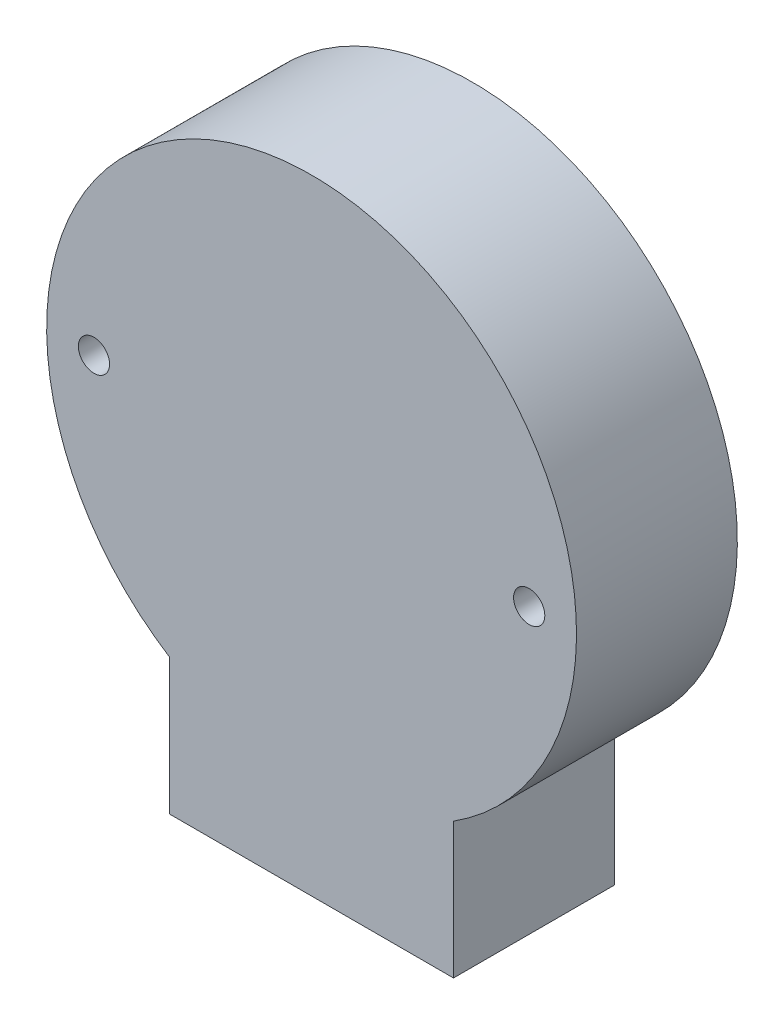
SolidWorks part; units mm, degrees
material "PF"
ref_plane "Front Plane" through (0, 0, 0) normal (0, 0, 1) x (1, 0, 0)
ref_plane "Top Plane" through (0, 0, 0) normal (0, 1, 0) x (1, 0, 0)
ref_plane "Right Plane" through (0, 0, 0) normal (1, 0, 0) x (0, 0, -1)
sketch "Sketch1" plane through (0, 0, 0) normal (0, 0, 1) x (1, 0, 0)
  line L0 (-24.6127, 28) -> (29.3258, 28) construction
  line L2 (-15, -23.6432) -> (-15, -38)
  line L3 (-15, -38) -> (15, -38)
  line L4 (15, -23.6432) -> (15, -38)
  arc A0 (15, -23.6432) -> (-15, -23.6432) centre (0, 0) ccw
  dimension "D1" = 56
  dimension "D2" = 66
  dimension "D3" = 30
extrude "Boss-Extrude1" add sketch "Sketch1" along normal blind 17
hole_wizard "Ø3.3 (3.3) Diameter Hole1" positions "Sketch3" profile "Sketch2" hole size "Ø3.3" standard "Ansi Metric"
sketch "Sketch3" plane through (0, 0, 17) normal (0, 0, 1) x (1, 0, 0)
  line L2 (-23, 0) -> (23, 0) construction
  point P0 (-23, 0)
  point P7 (23, 0)
  dimension "D1" = 46
sketch "Sketch2" plane through (-23, 0, 17) normal (1, 0, 0) x (0, -1, 0)
  line L0 (0, 0) -> (0, 25.9914)
  line L1 (0, 25.9914) -> (1.65, 25)
  line L2 (1.65, 25) -> (1.65, 0)
  line L5 (1.65, 0) -> (0, 0)
  line L10 (0, 25.9914) -> (-1.65, 25) construction
  line L11 (0, -6.35) -> (0, 107.95) construction
  dimension "Hole Dia." = 3.3
  dimension "Hole Depth" = 25
  dimension "Drill Angle" = 118
